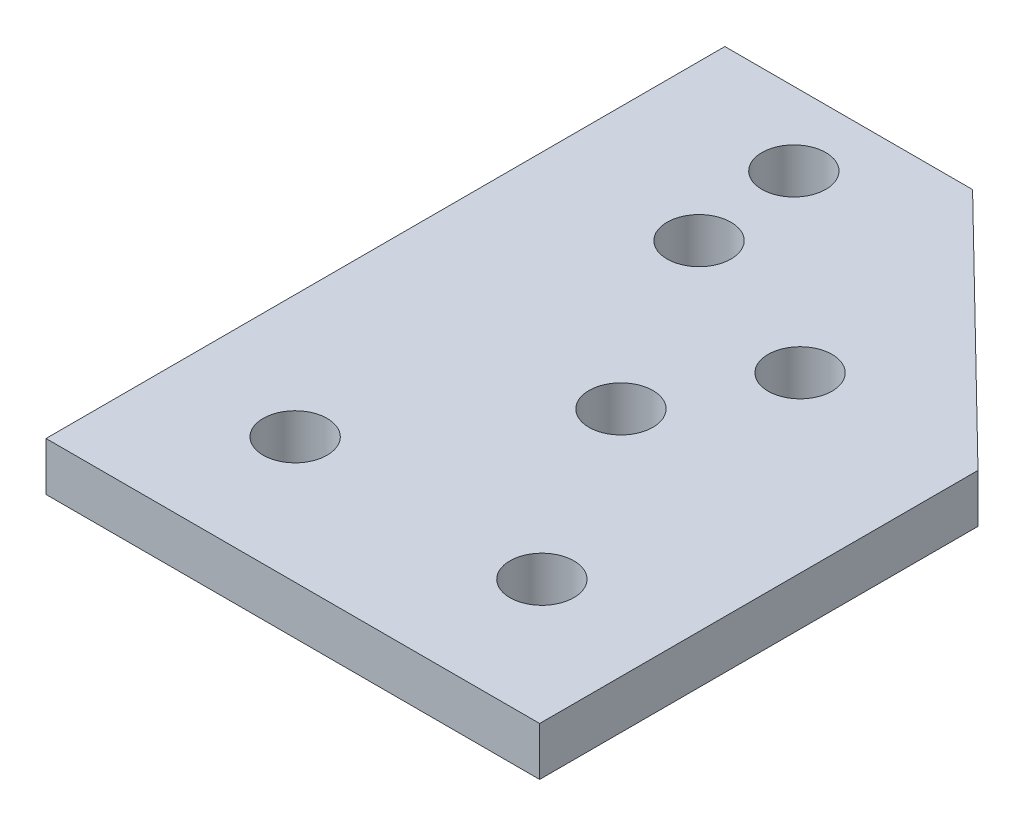
SolidWorks part; units mm, degrees
ref_plane "Front Plane" through (0, 0, 0) normal (0, 0, 1) x (1, 0, 0)
ref_plane "Top Plane" through (0, 0, 0) normal (0, 1, 0) x (1, 0, 0)
ref_plane "Right Plane" through (0, 0, 0) normal (1, 0, 0) x (0, 0, -1)
sketch "Sketch1" plane through (0, 0, 0) normal (0, 1, 0) x (1, 0, 0)
  line L0 (0, 0) -> (0, 70)
  line L1 (0, 70) -> (25.54, 70)
  line L2 (25.54, 70) -> (50.9, 45.2)
  line L3 (50.9, 45.2) -> (50.9, 0)
  line L4 (50.9, 0) -> (0, 0)
  line L5 (12.695, 12.995) -> (38.135, 12.995) construction
  line L6 (14.6675, 62.445) -> (38.135, 12.995) construction
  line L7 (38.135, 12.995) -> (16, 51.3339)
  circle A0 centre (14.6675, 62.445) radius 3.295
  circle A1 centre (33.0089, 44.7438) radius 3.295
  circle A2 centre (12.695, 12.995) radius 3.295
  circle A3 centre (38.135, 12.995) radius 3.295
  circle A4 centre (16, 51.3339) radius 3.295
  circle A5 centre (27, 32.2814) radius 3.295
  point P18 (25.54, 33.9224)
  dimension "D4" = 6.59
  dimension "D1" = 9.7
  dimension "D2" = 9.4
  dimension "D3" = 18.85
  dimension "D5" = 28.865
  dimension "D6" = 18.9
  dimension "D7" = 70
  dimension "D8" = 50.9
  dimension "D9" = 4.26
  dimension "D10" = 25.54
  dimension "D11" = 9.54
  dimension "D12" = 45.2
  dimension "D13" = 60
  dimension "D15" = 25.44
  dimension "D14" = 16
  dimension "D16" = 27
extrude "Boss-Extrude1" add sketch "Sketch1" along normal blind 5
equation "\"D5@Sketch1\"=25.57+\"D4@Sketch1\"/2"
